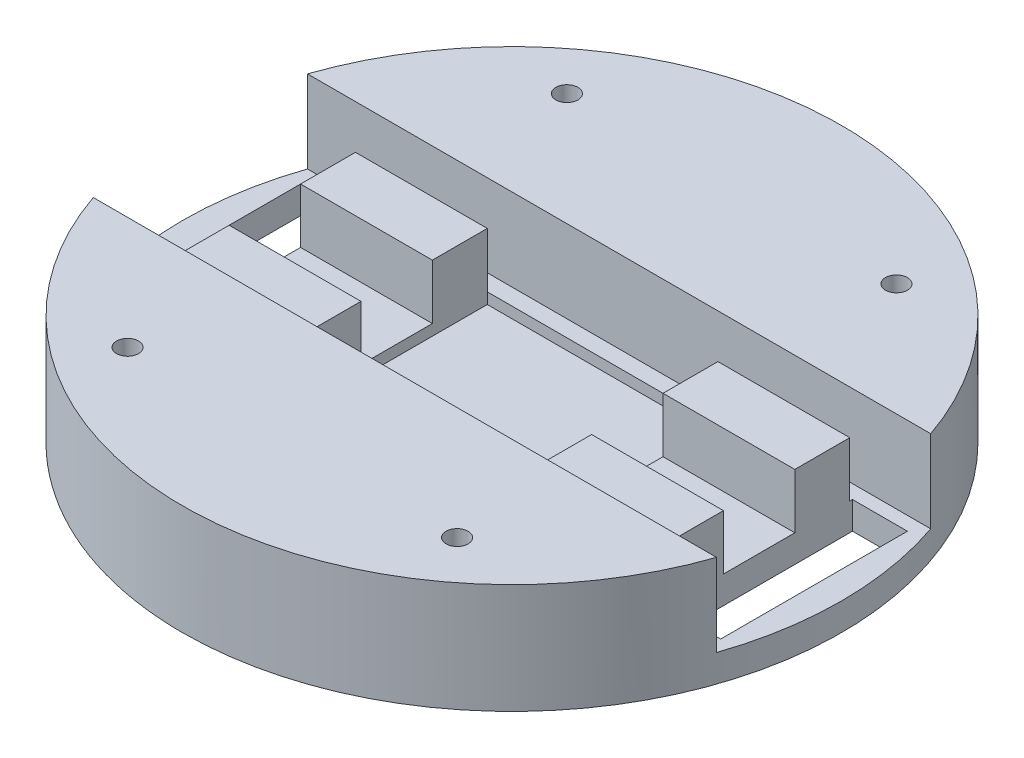
SolidWorks part; units mm, degrees
ref_plane "Front Plane" through (0, 0, 0) normal (0, 0, 1) x (1, 0, 0)
ref_plane "Top Plane" through (0, 0, 0) normal (0, 1, 0) x (1, 0, 0)
ref_plane "Right Plane" through (0, 0, 0) normal (1, 0, 0) x (0, 0, -1)
sketch "Sketch1" plane through (0, 0, 0) normal (0, 1, 0) x (1, 0, 0)
  circle A0 centre (0, 0) radius 60
  dimension "D1" = 120
extrude "Boss-Extrude1" add sketch "Sketch1" along normal blind 5
sketch "Sketch2" plane through (0, 5, 0) normal (0, 1, 0) x (1, 0, 0)
  line L0 (-45, 0) -> (-5, 0) construction
  line L1 (-45, 17) -> (-55, 17)
  line L2 (-45, 17) -> (-45, -17)
  line L3 (-45, -17) -> (-55, -17)
  line L4 (-55, 17) -> (-55, -17)
  line L5 (-55, 0) -> (-60, 0) construction
  line L6 (0, 0) -> (0, 50000) construction
  line L7 (55, 0) -> (60, 0) construction
  line L8 (45, 0) -> (5, 0) construction
  line L9 (55, 17) -> (55, -17)
  line L10 (45, -17) -> (55, -17)
  line L11 (45, 17) -> (45, -17)
  line L12 (45, 17) -> (55, 17)
  circle A0 centre (0, 0) radius 60 construction
  point P4 (-45, 0)
  dimension "D1" = 34
  dimension "D2" = 10
  dimension "D3" = 40
  dimension "D4" = 5
extrude "Cut-Extrude1" cut sketch "Sketch2" against normal through all both and the other way through all
sketch "Sketch3" plane through (0, 5, 0) normal (0, 1, 0) x (1, 0, 0)
  line L0 (-45, -17) -> (-45, 17) construction
  line L1 (-45, -6.5) -> (-21, -6.5)
  line L2 (-45, -6.5) -> (-45, -16.5)
  line L3 (-45, -16.5) -> (-21, -16.5)
  line L4 (-21, -6.5) -> (-21, -16.5)
  line L5 (-45, 16.5) -> (-21, 16.5)
  line L6 (-45, 16.5) -> (-45, 6.5)
  line L7 (-45, 6.5) -> (-21, 6.5)
  line L8 (-21, 16.5) -> (-21, 6.5)
  line L9 (-45, 6.5) -> (-45, -6.5) construction
  line L10 (0, 0) -> (0, -50000) construction
  line L11 (45, -16.5) -> (21, -16.5)
  line L12 (21, -6.5) -> (21, -16.5)
  line L13 (45, -6.5) -> (21, -6.5)
  line L14 (45, -6.5) -> (45, -16.5)
  line L15 (45, 6.5) -> (21, 6.5)
  line L16 (21, 16.5) -> (21, 6.5)
  line L17 (45, 16.5) -> (21, 16.5)
  line L18 (45, 16.5) -> (45, 6.5)
  point P10 (-45, 0)
  dimension "D1" = 13
  dimension "D2" = 10
  dimension "D3" = 24
extrude "Boss-Extrude2" add sketch "Sketch3" along normal blind 10
sketch "Sketch4" plane through (0, 5, 0) normal (0, 1, 0) x (1, 0, 0)
  line L1 (-21, 16.5) -> (21, 16.5)
  line L2 (-21, 16.5) -> (-21, -16.5)
  line L3 (-21, -16.5) -> (21, -16.5)
  line L4 (21, 16.5) -> (21, -16.5)
extrude "Cut-Extrude2" cut sketch "Sketch4" against normal blind 2
sketch "Sketch5" plane through (0, 5, 0) normal (0, 1, 0) x (1, 0, 0)
  line L0 (-56.7428, 19.5) -> (56.7428, 19.5)
  line L1 (-45, 17) -> (-55, 17) construction
  line L2 (-56.7428, -19.5) -> (56.7428, -19.5)
  line L3 (-55, -17) -> (-45, -17) construction
  circle A0 centre (0, 0) radius 60 construction
  circle A1 centre (0, 0) radius 60 construction
  arc A2 (-56.7428, 19.5) -> (56.7428, 19.5) centre (0, 0) cw
  arc A3 (-56.7428, -19.5) -> (56.7428, -19.5) centre (0, 0) ccw
  dimension "D1" = 2.5
  dimension "D2" = 2.5
extrude "Boss-Extrude3" add sketch "Sketch5" along normal blind 15
sketch "Sketch6" plane through (0, 20, 0) normal (0, 1, 0) x (1, 0, 0)
  circle A0 centre (30, -40) radius 2 construction
  circle A1 centre (-30, -40) radius 2 construction
  circle A2 centre (30, 40) radius 2 construction
  circle A3 centre (-30, 40) radius 2 construction
  circle A4 centre (30, -40) radius 2
  circle A5 centre (-30, -40) radius 2
  circle A6 centre (30, 40) radius 2
  circle A7 centre (-30, 40) radius 2
extrude "Cut-Extrude3" cut sketch "Sketch6" against normal blind 10
sketch "Sketch7" plane through (0, 0, 0) normal (1, 0, 0) x (0, 0, -1)
  line L0 (-60, 0) -> (-19.5, 0) construction
  line L1 (-60, 0) -> (60, 0) construction
  line L2 (-39.75, 0) -> (-39.75, -6.5)
  line L3 (-39.75, 0) -> (-19.5, 0)
  circle A0 centre (0, 10) radius 17 construction
  circle A1 centre (0, 10) radius 17 construction
  arc A2 (-39.75, -6.5) -> (-19.5, 0) centre (-39.8163, 28.4999) ccw
  dimension "D2" = 6.5
  dimension "D3" = 35
  dimension "D1" = 40.5
revolve "Revolve1" add sketch "Sketch7" angle 360 about L2
